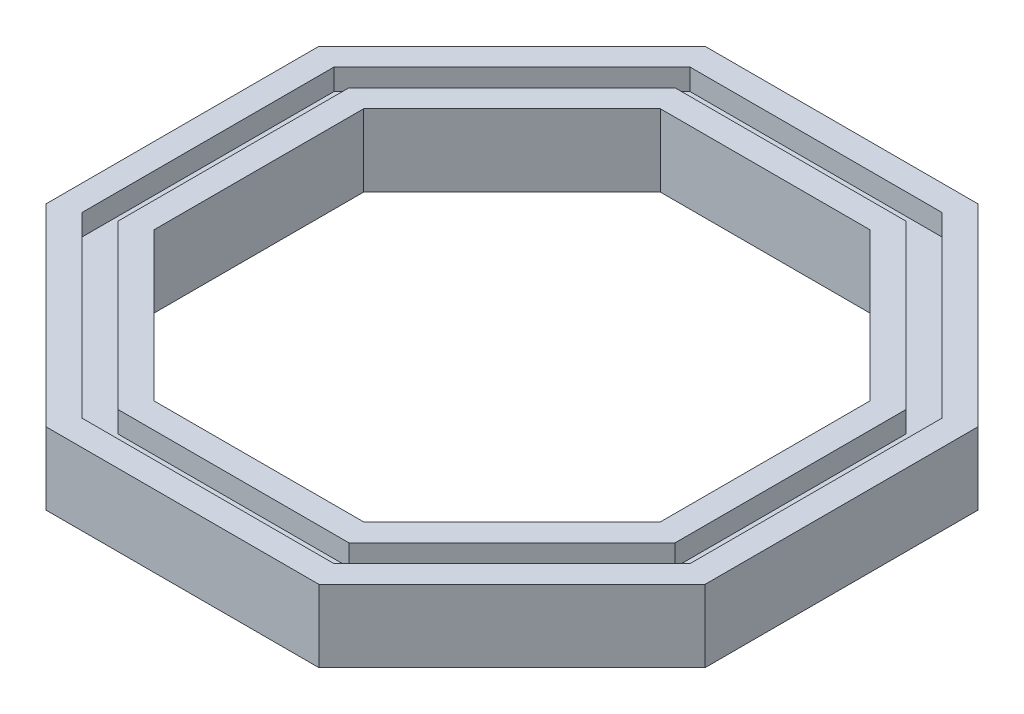
SolidWorks part; units mm, degrees
ref_plane "정면" through (0, 0, 0) normal (0, 0, 1) x (1, 0, 0)
ref_plane "윗면" through (0, 0, 0) normal (0, 1, 0) x (1, 0, 0)
ref_plane "우측면" through (0, 0, 0) normal (1, 0, 0) x (0, 0, -1)
sketch "스케치1" plane through (0, 0, 0) normal (0, 1, 0) x (1, 0, 0)
  line L0 (-55, 0) -> (55, 0) construction
  line L1 (5.9316, -14.3201) -> (14.3201, -5.9316)
  line L2 (14.3201, -5.9316) -> (14.3201, 5.9316)
  line L3 (14.3201, 5.9316) -> (5.9316, 14.3201)
  line L4 (5.9316, 14.3201) -> (-5.9316, 14.3201)
  line L5 (-5.9316, 14.3201) -> (-14.3201, 5.9316)
  line L6 (-14.3201, 5.9316) -> (-14.3201, -5.9316)
  line L7 (-14.3201, -5.9316) -> (-5.9316, -14.3201)
  line L8 (-5.9316, -14.3201) -> (5.9316, -14.3201)
  line L9 (6.4286, -15.5201) -> (15.5201, -6.4286)
  line L10 (15.5201, -6.4286) -> (15.5201, 6.4286)
  line L11 (15.5201, 6.4286) -> (6.4286, 15.5201)
  line L12 (6.4286, 15.5201) -> (-6.4286, 15.5201)
  line L13 (-6.4286, 15.5201) -> (-15.5201, 6.4286)
  line L14 (-15.5201, 6.4286) -> (-15.5201, -6.4286)
  line L15 (-15.5201, -6.4286) -> (-6.4286, -15.5201)
  line L16 (-6.4286, -15.5201) -> (6.4286, -15.5201)
  line L17 (5.4345, -13.1201) -> (13.1201, -5.4345)
  line L18 (13.1201, -5.4345) -> (13.1201, 5.4345)
  line L19 (13.1201, 5.4345) -> (5.4345, 13.1201)
  line L20 (5.4345, 13.1201) -> (-5.4345, 13.1201)
  line L21 (-5.4345, 13.1201) -> (-13.1201, 5.4345)
  line L22 (-13.1201, 5.4345) -> (-13.1201, -5.4345)
  line L23 (-13.1201, -5.4345) -> (-5.4345, -13.1201)
  line L24 (-5.4345, -13.1201) -> (5.4345, -13.1201)
  circle A0 centre (0, 0) radius 15.5 construction
  dimension "D1" = 31
  dimension "D2" = 1.2
  dimension "D3" = 1.2
extrude "보스-돌출1" add sketch "스케치1" along normal blind 1.7 contours L15 L16 L9 L10 L11 L12 L13 L14 L8 L7 L6 L5 L4 L3 L2 L1 | L7 L8 L1 L2 L3 L4 L5 L6 L24 L23 L22 L21 L20 L19 L18 L17 | L23 L24 L17 L18 L19 L20 L21 L22
sketch "스케치2" plane through (0, 1.7, 0) normal (0, 1, 0) x (1, 0, 0)
  line L8 (-13.1201, -5.4345) -> (-5.4345, -13.1201)
  line L9 (-5.4345, -13.1201) -> (5.4345, -13.1201)
  line L10 (5.4345, -13.1201) -> (13.1201, -5.4345)
  line L11 (13.1201, -5.4345) -> (13.1201, 5.4345)
  line L12 (13.1201, 5.4345) -> (5.4345, 13.1201)
  line L13 (5.4345, 13.1201) -> (-5.4345, 13.1201)
  line L14 (-5.4345, 13.1201) -> (-13.1201, 5.4345)
  line L15 (-13.1201, 5.4345) -> (-13.1201, -5.4345)
  line L16 (-14.3201, -5.9316) -> (-5.9316, -14.3201)
  line L17 (-5.9316, -14.3201) -> (5.9316, -14.3201)
  line L18 (5.9316, -14.3201) -> (14.3201, -5.9316)
  line L19 (14.3201, -5.9316) -> (14.3201, 5.9316)
  line L20 (14.3201, 5.9316) -> (5.9316, 14.3201)
  line L21 (5.9316, 14.3201) -> (-5.9316, 14.3201)
  line L22 (-5.9316, 14.3201) -> (-14.3201, 5.9316)
  line L23 (-14.3201, 5.9316) -> (-14.3201, -5.9316)
  line L24 (-14.3201, -5.9316) -> (-5.9316, -14.3201)
  line L25 (-5.9316, -14.3201) -> (5.9316, -14.3201)
  line L26 (5.9316, -14.3201) -> (14.3201, -5.9316)
  line L27 (14.3201, -5.9316) -> (14.3201, 5.9316)
  line L28 (14.3201, 5.9316) -> (5.9316, 14.3201)
  line L29 (5.9316, 14.3201) -> (-5.9316, 14.3201)
  line L30 (-5.9316, 14.3201) -> (-14.3201, 5.9316)
  line L31 (-14.3201, 5.9316) -> (-14.3201, -5.9316)
  dimension "D1" = 1.2
  dimension "D2" = 1.2
extrude "컷-돌출3" cut sketch "스케치2" against normal blind 1
sketch "스케치3" plane through (0, 1.7, 0) normal (0, 1, 0) x (1, 0, 0)
  line L16 (-4.9375, 11.9201) -> (-11.9201, 4.9375)
  line L17 (-11.9201, 4.9375) -> (-11.9201, -4.9375)
  line L18 (-11.9201, -4.9375) -> (-4.9375, -11.9201)
  line L19 (-4.9375, -11.9201) -> (4.9375, -11.9201)
  line L20 (4.9375, -11.9201) -> (11.9201, -4.9375)
  line L21 (11.9201, -4.9375) -> (11.9201, 4.9375)
  line L22 (11.9201, 4.9375) -> (4.9375, 11.9201)
  line L23 (4.9375, 11.9201) -> (-4.9375, 11.9201)
  line L24 (-4.9375, 11.9201) -> (-11.9201, 4.9375)
  line L25 (-11.9201, 4.9375) -> (-11.9201, -4.9375)
  line L26 (-11.9201, -4.9375) -> (-4.9375, -11.9201)
  line L27 (-4.9375, -11.9201) -> (4.9375, -11.9201)
  line L28 (4.9375, -11.9201) -> (11.9201, -4.9375)
  line L29 (11.9201, -4.9375) -> (11.9201, 4.9375)
  line L30 (11.9201, 4.9375) -> (4.9375, 11.9201)
  line L31 (4.9375, 11.9201) -> (-4.9375, 11.9201)
  dimension "D1" = 1.2
extrude "컷-돌출4" cut sketch "스케치3" against normal through all
mirror "대칭 복사1" about plane through (0, 0, 0) normal (0, 1, 0) of "컷-돌출4", "컷-돌출3", "보스-돌출1"
